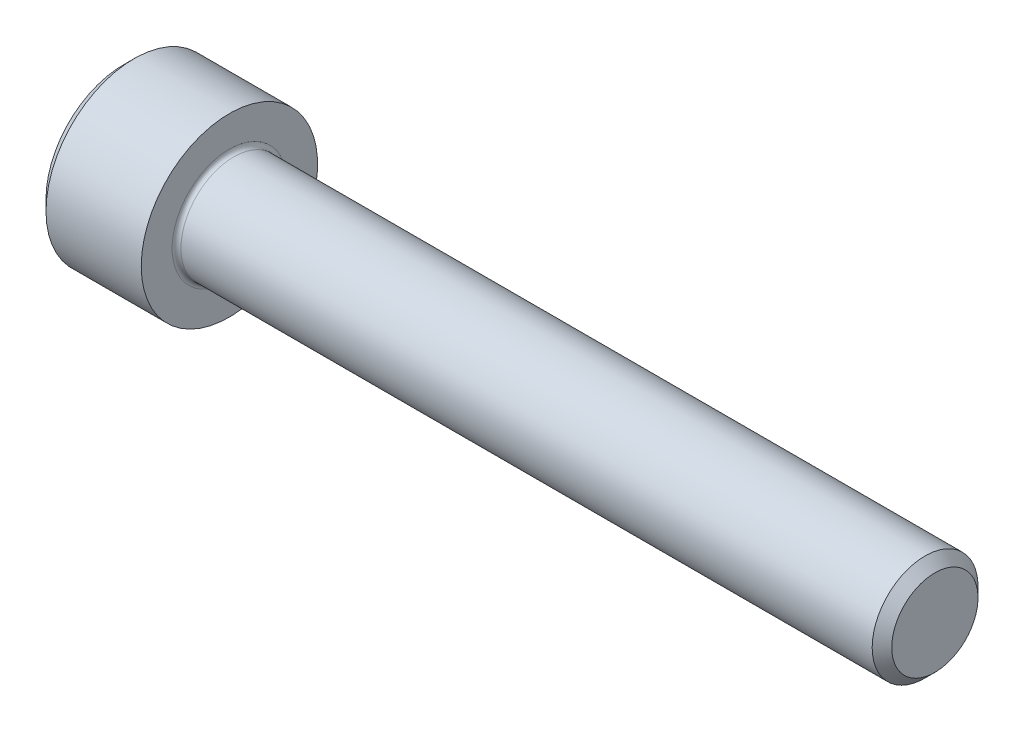
SolidWorks part; units mm, degrees
revolve "Base-Revolve" add sketch "BodySke"
sketch "BodySke" plane through (0, 0, 0) normal (0, 0, 1) x (1, 0, 0)
  line L0 (0, 0) -> (0, 4.4)
  line L1 (0.6, 5) -> (6, 5)
  line L2 (6, 5) -> (6, 3)
  line L3 (6, 3) -> (45.4455, 3)
  line L4 (46, 2.4455) -> (46, 0)
  line L5 (46, 0) -> (0, 0)
  line L6 (-31.75, 0) -> (127, 0) construction
  line L7 (0, 4.4) -> (0.6, 5)
  line L8 (46, 2.4455) -> (45.4455, 3)
  line L9 (0, -4.4) -> (0.6, -5) construction
  line L10 (46, -2.4455) -> (45.4455, -3) construction
  line L11 (7, 9.525) -> (7, 3.175) construction
  line L12 (22, 9.525) -> (22, 3.175) construction
  line L13 (6, 9.525) -> (6, 3.175) construction
  dimension "Diameter" = 6
  dimension "Head_ht" = 6
  dimension "Length" = 40
  dimension "Body_ch_ang" = 45
  dimension "Head_dia" = 10
  dimension "Head_ch_ang" = 45
  dimension "Minor_dia" = 4.891
  dimension "Advance" = 1
  dimension "Thread_nom" = 24
  dimension "Thread_length" = 40
  dimension "Head_ch_ht" = 0.6
cosmetic thread "ThreadCosmetic" [suppressed]
fillet "Fillet1" radius 0.25 1 edges at (6, 0, 3)
ref_plane "Plane1" through (0, 0, 0) normal (0, 0, 1) x (1, 0, 0)
ref_plane "Plane2" through (0, 0, 0) normal (0, 1, 0) x (1, 0, 0)
ref_plane "Plane3" through (0, 0, 0) normal (1, 0, 0) x (0, 0, -1)
sketch "Sketch2" plane through (0, 0, 0) normal (0, 0, 1) x (1, 0, 0)
  line L0 (0, 2.542) -> (3, 2.542)
  line L1 (3, 2.542) -> (4.4676, 0)
  line L2 (-31.75, 0) -> (127, 0) construction
  line L3 (4.4676, 0) -> (0, 0)
  line L4 (0, 0) -> (0, 2.542)
  line L5 (0, 4.4) -> (0, -4.4) construction
  line L6 (0, 0) -> (47.625, 0) construction
  line L7 (6, -5) -> (6, 5) construction
  dimension "D1" = 2.542
  dimension "D2" = 60
revolve "Hex-PreBroach" cut sketch "Sketch2" angle 360 about L6
sketch "Sketch3" plane through (0, 0, 0) normal (-1, 0, 0) x (0, 0.5, 0.866)
  line L0 (1.4676, 2.542) -> (-1.4676, 2.542)
  line L1 (-1.4676, 2.542) -> (-2.9352, 0)
  line L2 (1.4676, 2.542) -> (2.9352, 0)
  line L3 (1.4676, -2.542) -> (2.9352, 0)
  line L4 (1.4676, -2.542) -> (-1.4676, -2.542)
  line L5 (-1.4676, -2.542) -> (-2.9352, 0)
  dimension "D1" = 2.542
  dimension "D2" = 2.542
  dimension "Hex_size" = 5.084
extrude "Hex" cut sketch "Sketch3" against normal blind 3
sketch "Sketch4" plane through (0, 0, 0) normal (-1, 0, 0) x (0, 0, 1)
  line L0 (0, 0) -> (2.8067, 0)
  line L1 (0, 0) -> (6.1484, 3.5498) construction
  line L2 (0, 0) -> (1.4033, 2.4307)
  line L3 (2.3336, 0.614) -> (2.6851, 0.817)
  line L4 (1.6986, 1.7139) -> (2.0501, 1.9169)
  arc A0 (2.3336, 0.614) -> (1.6986, 1.7139) centre (0, 0) ccw
  arc A1 (2.8067, 0) -> (2.6851, 0.817) centre (0, 0) ccw
  arc A2 (1.4033, 2.4307) -> (2.0501, 1.9169) centre (0, 0) cw
  dimension "D1" = 30
  dimension "D2" = 60
  dimension "Spline_p_dim" = 1.27
  dimension "D3" = 0.635
extrude "Spline" [suppressed] cut sketch "Sketch4" against normal blind 3
pattern_circular "CirPattern1" [suppressed] count 6 every 60
sketch "Sketch5" plane through (0, 0, 0) normal (0, 0, 1) x (1, 0, 0)
  line L0 (-31.75, 0) -> (127, 0) construction
  line L2 (0, 4.4) -> (0, -4.4) construction
  circle A0 centre (2.3, 0) radius 0.675
  dimension "Drilled_hole_dia" = 1.35
  dimension "Drilled_hole_loc" = 2.3
extrude "Hole" [suppressed] cut sketch "Sketch5" against normal through all and the other way through all
pattern_circular "Drilled-4" [suppressed] count 2 every 60
pattern_circular "Drilled-6" [suppressed] count 3 every 60
sketch "ThdSchSke" plane through (0, 0, 0) normal (0, 0, 1) x (1, 0, 0)
  line L0 (22, -2.4455) -> (21.6117, -3)
  line L1 (22, -2.4455) -> (22.3883, -3)
  line L2 (22.3883, -3) -> (22.3883, -3.75)
  line L3 (-3.175, 0) -> (5.1513, 0) construction
  line L5 (22.3883, -3.75) -> (21.6117, -3.75)
  line L6 (21.6117, -3.75) -> (21.6117, -3)
  line L7 (0, 4.4) -> (0, -4.4) construction
  dimension "Thread_minor" = 4.891
  dimension "Diameter" = 6
  dimension "Start" = 22
revolve "ThreadSchematic" [suppressed] cut sketch "ThdSchSke" angle 360 about L3
pattern_linear "ThdSchPat" [suppressed]
equation "\"D2@Sketch3\" = \"Hex_size@Sketch3\" / 2"
equation "\"D1@Sketch3\" = \"Hex_size@Sketch3\" / 2"
equation "\"D1@Sketch2\" = \"Hex_size@Sketch3\" / 2"
equation "\"D3@Sketch4\" = \"Spline_p_dim@Sketch4\" / 2"
equation "\"Thread_minor@ThreadCosmetic\"  =  \"Minor_dia@BodySke\""
equation "\"D2@CirPattern1\" = 360 / \"Num_teeth@CirPattern1\""
equation "\"Wall_thickness@Sketch2\" = \"Head_ht@BodySke\" - \"Key_eng@Hex\""
equation "\"Thread_length@ThreadCosmetic\" = ((sgn( (\"Length@BodySke\" - \"Advance@BodySke\" ) - \"Thread_nom@BodySke\" )-1)*( (\"Length@BodySke\" - \"Advance@BodySke\" ) - \"Thread_nom@BodySke\" ))/-2+ \"Thread_nom@BodySke\""
equation "\"Thread_minor@ThdSchSke\" = \"Minor_dia@BodySke\""
equation "\"Diameter@ThdSchSke\" = \"Diameter@BodySke\""
equation "\"Overcut@ThdSchSke\" = \"Diameter@BodySke\" * 1.25"
equation "\"Start@ThdSchSke\" = \"Head_ht@BodySke\" + \"Length@BodySke\" - \"Thread_length@ThreadCosmetic\"  '---Non-countersunk---"
equation "\"Num_threads@ThdSchPat\" = int( \"Thread_length@ThreadCosmetic\" / \"Advance@BodySke\" + 0.999 )  + 1"
equation "\"Advance@ThdSchPat\" = \"Thread_length@ThreadCosmetic\" /  (\"Num_threads@ThdSchPat\" - 1) 'relax it"
equation "\"Num_threads@ThdSchPat\" = \"Num_threads@ThdSchPat\" - sgn( \"Num_threads@ThdSchPat\" - 1) '---chamfered tips only---"
